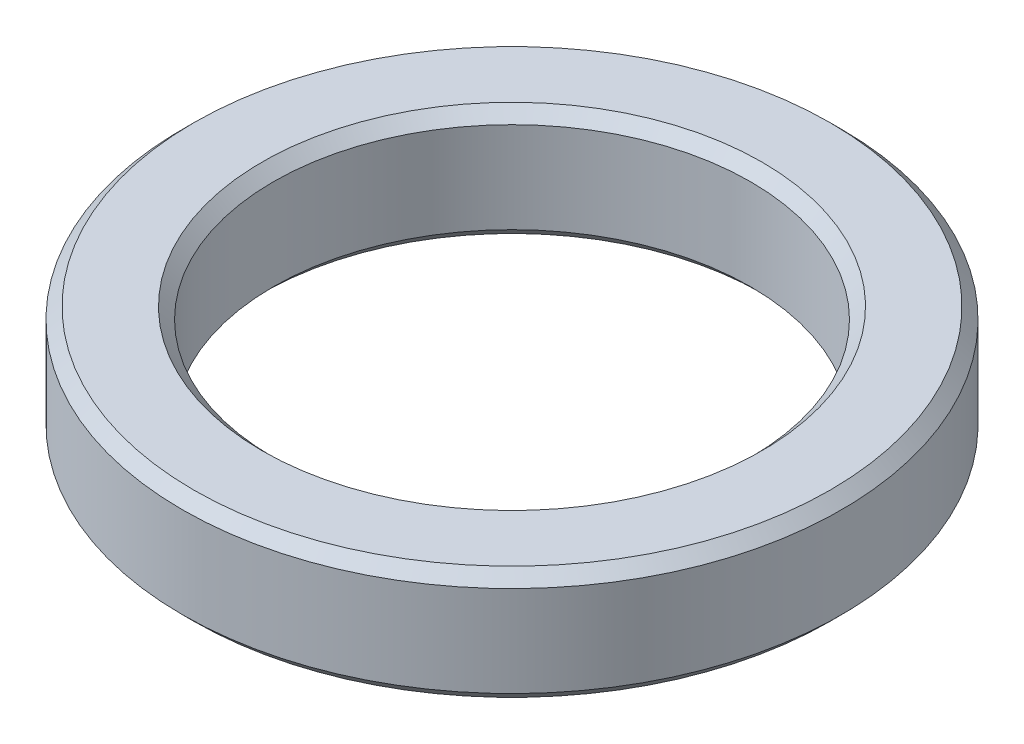
SolidWorks part; units mm, degrees
material "普通碳钢"
ref_plane "前视基准面" through (0, 0, 0) normal (0, 0, 1) x (1, 0, 0)
ref_plane "上视基准面" through (0, 0, 0) normal (0, 1, 0) x (1, 0, 0)
ref_plane "右视基准面" through (0, 0, 0) normal (1, 0, 0) x (0, 0, -1)
sketch "草图2" plane through (0, 0, 0) normal (0, 1, 0) x (1, 0, 0)
  circle A0 centre (0, 0) radius 10.5
  circle A1 centre (0, 0) radius 14.5
  dimension "D1" = 21
  dimension "D2" = 4
extrude "凸台-拉伸1" add sketch "草图2" along normal blind 5
chamfer "倒角1" distance 0.5 angle 45 4 edges at (0, 0, 10.5) (0, 0, 14.5) (0, 5, 10.5) (0, 5, 14.5)
